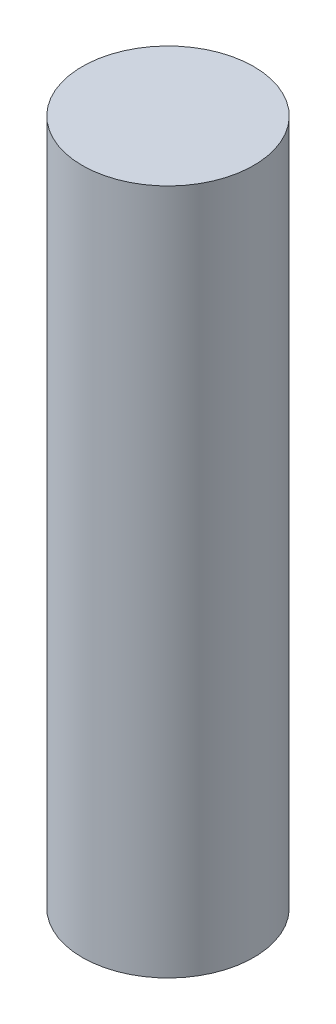
SolidWorks part; units mm, degrees
ref_plane "Front Plane" through (0, 0, 0) normal (0, 0, 1) x (1, 0, 0)
ref_plane "Top Plane" through (0, 0, 0) normal (0, 1, 0) x (1, 0, 0)
ref_plane "Right Plane" through (0, 0, 0) normal (1, 0, 0) x (0, 0, -1)
sketch "Sketch1" plane through (0, 0, 0) normal (0, 1, 0) x (1, 0, 0)
  circle A0 centre (0, 0) radius 3.175
  dimension "D1" = 6.35
extrude "Boss-Extrude1" add sketch "Sketch1" along normal mid plane 25.4
